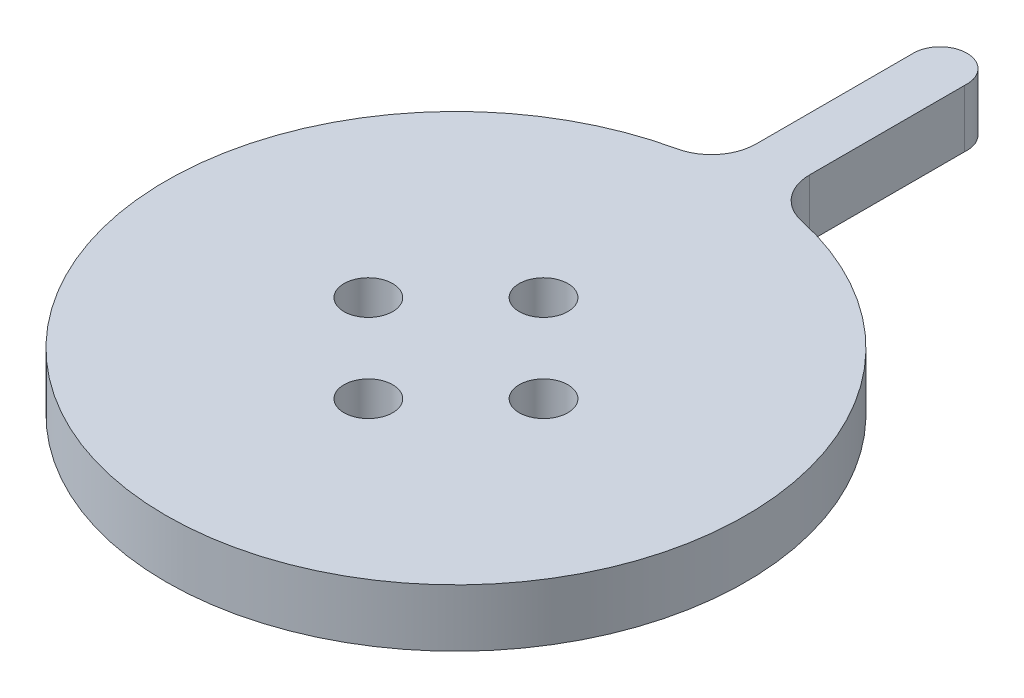
SolidWorks part; units mm, degrees
ref_plane "Front Plane" through (0, 0, 0) normal (0, 0, 1) x (1, 0, 0)
ref_plane "Top Plane" through (0, 0, 0) normal (0, 1, 0) x (1, 0, 0)
ref_plane "Right Plane" through (0, 0, 0) normal (1, 0, 0) x (0, 0, -1)
sketch "Sketch2" plane through (0, 0, 0) normal (0, 1, 0) x (1, 0, 0)
  circle A0 centre (0, 0) radius 32.768
extrude "Boss-Extrude1" add sketch "Sketch2" along normal blind 5
sketch "Sketch3" plane through (0, 0, 0) normal (0, -1, 0) x (1, 0, 0)
  circle A0 centre (0, 0) radius 32.768
  circle A1 centre (0, 0) radius 30.268
extrude "Boss-Extrude2" add sketch "Sketch3" along normal blind 1.5
sketch "Sketch4" plane through (0, 5, 0) normal (0, 1, 0) x (1, 0, 0)
  circle A9 centre (0, 9.8995) radius 2.75
  circle A10 centre (-9.9, 0) radius 2.75
  circle A11 centre (9.9, 0) radius 2.75
  circle A12 centre (0, -9.9) radius 2.75
  dimension "D3" = 9.9
  dimension "D1" = 9.8995
  dimension "D2" = 9.9
  dimension "D4" = 9.9
extrude "Cut-Extrude1" cut sketch "Sketch4" against normal blind 9.8995
sketch "Sketch5" plane through (0, 5, 0) normal (0, 1, 0) x (1, 0, 0)
  line L1 (-3.0234, 36.9517) -> (-3.0234, 54.9517)
  line L3 (3.0234, 54.4772) -> (3.0234, 36.9517)
  arc A0 (-7, 32.0116) -> (7, 32.0116) centre (0, 0) cw
  circle A1 centre (0, 0) radius 32.768 construction
  arc A2 (-7, 32.0116) -> (-3.0234, 36.9517) centre (-8.0803, 36.9517) ccw
  arc A3 (7, 32.0116) -> (3.0234, 36.9517) centre (8.0803, 36.9517) cw
  arc A4 (3.0234, 54.4772) -> (-3.0234, 54.9517) centre (0, 54.7144) ccw
  dimension "D1" = 18
extrude "Boss-Extrude3" add sketch "Sketch5" against normal blind 6.5
